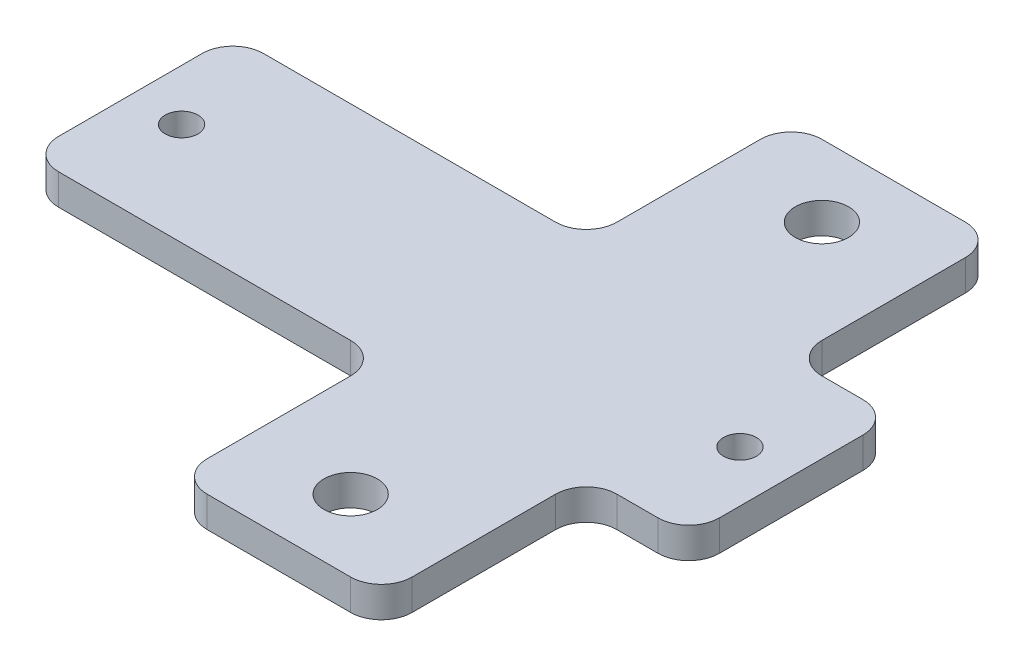
SolidWorks part; units mm, degrees
material "A-玻璃纤维"
ref_plane "前视基准面" through (0, 0, 0) normal (0, 0, 1) x (1, 0, 0)
ref_plane "上视基准面" through (0, 0, 0) normal (0, 1, 0) x (1, 0, 0)
ref_plane "右视基准面" through (0, 0, 0) normal (1, 0, 0) x (0, 0, -1)
sketch "草图1" plane through (0, 0, 0) normal (0, 1, 0) x (1, 0, 0)
  line L0 (10, 60) -> (10, 0) construction
  line L1 (0, 0) -> (20, 0)
  line L2 (0, 0) -> (0, 60)
  line L3 (0, 60) -> (20, 60)
  line L4 (20, 0) -> (20, 60)
  line L5 (0, 30) -> (20, 30) construction
  circle A0 centre (10, 7) radius 2.6
  circle A1 centre (10, 53) radius 2.6
  dimension "D3" = 5.2
  dimension "D4" = 46
  dimension "D1" = 20
  dimension "D2" = 60
extrude "凸台-拉伸1" add sketch "草图1" along normal blind 3
sketch "草图2" plane through (0, 3, 0) normal (0, 1, 0) x (1, 0, 0)
  line L0 (0, 30) -> (-34.5, 30) construction
  line L1 (0, 60) -> (0, 0) construction
  line L2 (20, 30) -> (39.2088, 30) construction
  line L3 (0, 20) -> (-34.5, 20)
  line L4 (0, 20) -> (0, 40)
  line L5 (0, 40) -> (-34.5, 40)
  line L6 (-34.5, 20) -> (-34.5, 40)
  line L7 (20, 0) -> (20, 60) construction
  line L9 (20, 20) -> (30, 20)
  line L10 (20, 20) -> (20, 40)
  line L11 (20, 40) -> (30, 40)
  line L12 (30, 20) -> (30, 40)
  circle A0 centre (-29.5, 30) radius 1.6
  circle A1 centre (25, 30) radius 1.6
  dimension "D2" = 5
  dimension "D3" = 3.2
  dimension "D4" = 29.5
  dimension "D5" = 5
  dimension "D1" = 20
  dimension "D6" = 10
extrude "凸台-拉伸2" add sketch "草图2" against normal up to surface (3 mm away) up to face at (10, 0, -4.4)
fillet "圆角1" radius 3 12 edges at (-34.5, 1.5, -20) (-34.5, 1.5, -40) (0, 1.5, -40) (0, 1.5, -60) (20, 1.5, -60) (20, 1.5, -40) (30, 1.5, -40) (20, 1.5, -20) (30, 1.5, -20) (20, 1.5, 0) (0, 1.5, -20) (0, 1.5, 0)
